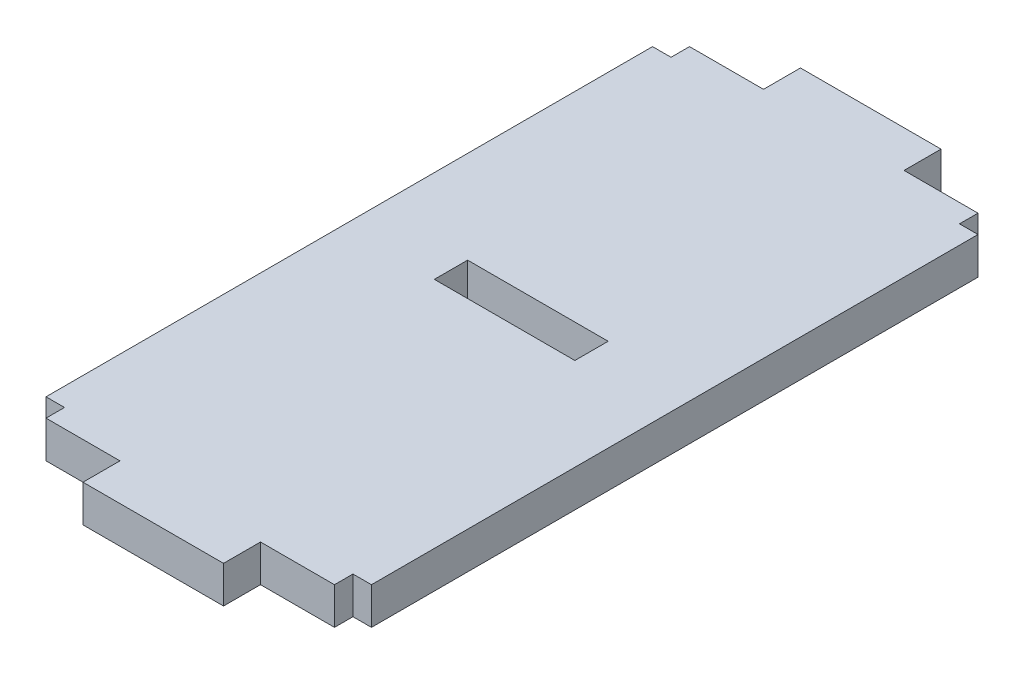
SolidWorks part; units mm, degrees
ref_plane "前视基准面" through (0, 0, 0) normal (0, 0, 1) x (1, 0, 0)
ref_plane "上视基准面" through (0, 0, 0) normal (0, 1, 0) x (1, 0, 0)
ref_plane "右视基准面" through (0, 0, 0) normal (1, 0, 0) x (0, 0, -1)
sketch "草图1" plane through (0, 0, 0) normal (0, 1, 0) x (1, 0, 0)
  line L0 (-2, -2) -> (19.6, -2) construction
  line L1 (0, 0) -> (17.6, 0)
  line L2 (0, 0) -> (0, 34.8)
  line L3 (0, 34.8) -> (17.6, 34.8)
  line L4 (17.6, 0) -> (17.6, 34.8)
  line L5 (19.6, -2) -> (19.6, 36.8) construction
  line L6 (-2, 36.8) -> (19.6, 36.8) construction
  line L7 (-2, -2) -> (-2, 36.8) construction
  line L8 (12.6, 5) -> (12.6, 29.8) construction
  line L9 (5, 29.8) -> (12.6, 29.8) construction
  line L10 (5, 5) -> (5, 29.8) construction
  line L11 (5, 5) -> (12.6, 5) construction
  line L12 (12.6, 5) -> (12.6, -4.6272) construction
  line L13 (5, 5) -> (5, -2) construction
  line L14 (-6.6019, 17) -> (28.6178, 17) construction
  line L15 (5, 0) -> (12.6, 0)
  line L16 (5, 0) -> (5, -2)
  line L17 (5, -2) -> (12.6, -2)
  line L18 (12.6, 0) -> (12.6, -2)
  line L19 (5, 36.8) -> (12.6, 36.8)
  line L20 (5, 36.8) -> (5, 34.8)
  line L21 (5, 34.8) -> (12.6, 34.8)
  line L22 (12.6, 36.8) -> (12.6, 34.8)
  line L23 (-6.6019, 18.8) -> (28.6178, 18.8) construction
  line L24 (-6.6019, 17) -> (28.6178, 17) construction
  line L25 (5, 18.8) -> (12.6, 18.8)
  line L26 (5, 18.8) -> (5, 17)
  line L27 (5, 17) -> (12.6, 17)
  line L28 (12.6, 18.8) -> (12.6, 17)
  line L30 (0, 34.8) -> (1, 34.8)
  line L31 (0, 34.8) -> (0, 33.8)
  line L32 (0, 33.8) -> (1, 33.8)
  line L33 (1, 34.8) -> (1, 33.8)
  line L34 (17.6, 34.8) -> (16.6, 34.8)
  line L35 (17.6, 34.8) -> (17.6, 33.8)
  line L36 (17.6, 33.8) -> (16.6, 33.8)
  line L37 (16.6, 34.8) -> (16.6, 33.8)
  line L38 (17.6, 0) -> (16.6, 0)
  line L39 (17.6, 0) -> (17.6, 1)
  line L40 (17.6, 1) -> (16.6, 1)
  line L41 (16.6, 0) -> (16.6, 1)
  line L42 (0, 0) -> (1, 0)
  line L43 (0, 0) -> (0, 1)
  line L44 (0, 1) -> (1, 1)
  line L45 (1, 0) -> (1, 1)
  dimension "D1" = 2
  dimension "D2" = 5
  dimension "D3" = 1.8
extrude "凸台-拉伸1" add sketch "草图1" along normal blind 2 contours L1 L4 L3 L2 L25 L28 L27 L26 | L18 L1 L16 L17 | L22 L19 L20 L3
